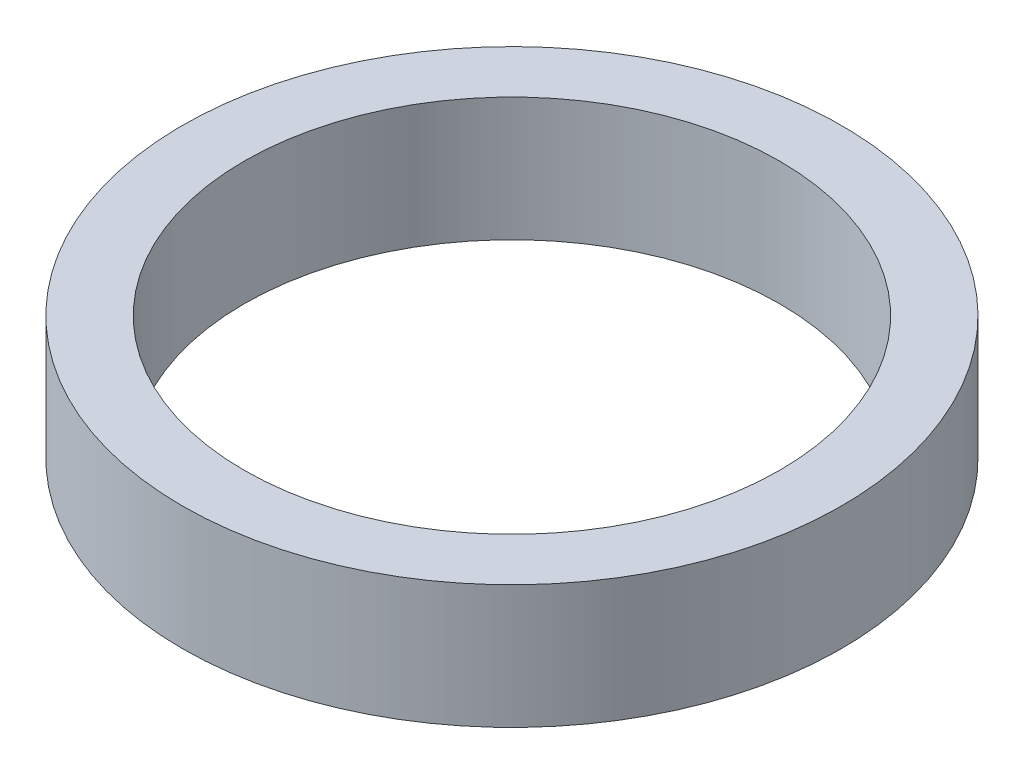
SolidWorks part; units mm, degrees
ref_plane "Front Plane" through (0, 0, 0) normal (0, 0, 1) x (1, 0, 0)
ref_plane "Top Plane" through (0, 0, 0) normal (0, 1, 0) x (1, 0, 0)
ref_plane "Right Plane" through (0, 0, 0) normal (1, 0, 0) x (0, 0, -1)
sketch "Sketch1" plane through (0, 0, 0) normal (0, 1, 0) x (1, 0, 0)
  circle A0 centre (0, 0) radius 6.5
  circle A1 centre (0, 0) radius 8
  dimension "D1" = 13
  dimension "D2" = 16
extrude "Boss-Extrude1" add sketch "Sketch1" along normal blind 3
